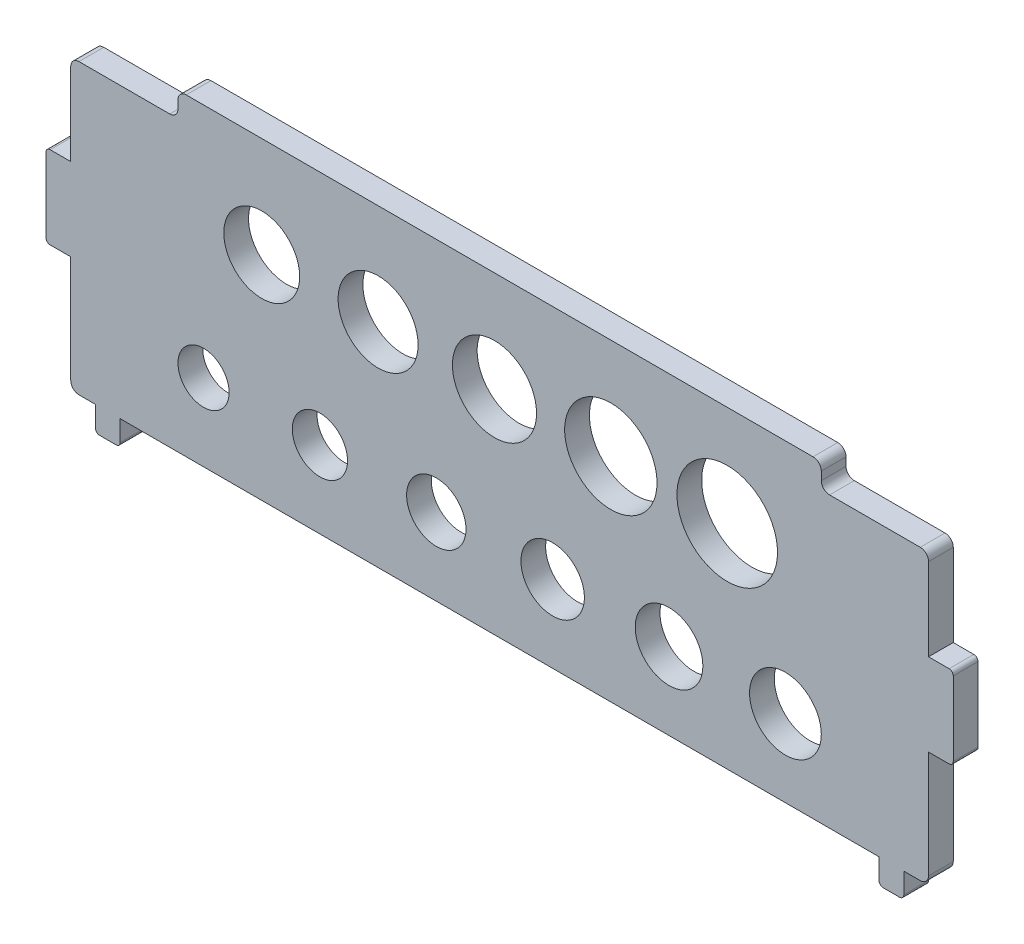
SolidWorks part; units mm, degrees
ref_plane "Спереди" through (0, 0, 0) normal (0, 0, 1) x (1, 0, 0)
ref_plane "Сверху" through (0, 0, 0) normal (0, 1, 0) x (1, 0, 0)
ref_plane "Справа" through (0, 0, 0) normal (1, 0, 0) x (0, 0, -1)
sketch "Эскиз1" plane through (0, 0, 0) normal (0, 0, 1) x (1, 0, 0)
  line L0 (0, 0) -> (0, 25.1439) construction
  line L1 (-52, 19) -> (52, 19)
  line L2 (-52, 19) -> (-52, -19)
  line L3 (-52, -19) -> (-49, -19)
  line L4 (52, 19) -> (52, -19)
  line L5 (-52, 19) -> (52, -19) construction
  line L6 (-52, -19) -> (52, 19) construction
  line L7 (52, 5) -> (55, 5)
  line L8 (52, 5) -> (52, -5)
  line L9 (52, -5) -> (55, -5)
  line L10 (55, 5) -> (55, -5)
  line L11 (52, 5) -> (55, -5) construction
  line L12 (52, -5) -> (55, 5) construction
  line L13 (-52, -5) -> (-55, 5) construction
  line L14 (-52, 5) -> (-55, -5) construction
  line L15 (-55, 5) -> (-55, -5)
  line L16 (-52, -5) -> (-55, -5)
  line L17 (-52, 5) -> (-52, -5)
  line L18 (-52, 5) -> (-55, 5)
  line L19 (-52, 16) -> (-39, 16)
  line L20 (-39, 16) -> (-39, 19)
  line L21 (39, 16) -> (39, 19)
  line L22 (52, 16) -> (39, 16)
  line L23 (27.595, 6.8) -> (27.595, -9.65) construction
  line L24 (27.595, 6.8) -> (13.485, 6.8) construction
  line L25 (13.485, 6.8) -> (-0.625, 6.8) construction
  line L26 (-0.625, 6.8) -> (-14.735, 6.8) construction
  line L27 (-14.735, 6.8) -> (-28.845, 6.8) construction
  line L28 (34.65, -9.65) -> (20.54, -9.65) construction
  line L29 (20.54, -9.65) -> (6.43, -9.65) construction
  line L30 (6.43, -9.65) -> (-7.68, -9.65) construction
  line L31 (-7.68, -9.65) -> (-21.79, -9.65) construction
  line L32 (-21.79, -9.65) -> (-35.9, -9.65) construction
  line L33 (0, -19) -> (46, -19)
  line L38 (49, -19) -> (52, -19)
  line L39 (-46, -19) -> (0, -19)
  line L40 (-49, -22) -> (-46, -19) construction
  line L42 (49, -19) -> (49, -22)
  line L43 (49, -22) -> (46, -22)
  line L44 (46, -19) -> (46, -22)
  line L45 (49, -19) -> (46, -22) construction
  line L46 (49, -22) -> (46, -19) construction
  line L47 (-49, -19) -> (-46, -22) construction
  line L48 (-46, -19) -> (-46, -22)
  line L49 (-49, -22) -> (-46, -22)
  line L50 (-49, -19) -> (-49, -22)
  circle A18 centre (27.595, 6.8) radius 6.1
  circle A19 centre (13.485, 6.8) radius 5.6
  circle A20 centre (-0.625, 6.8) radius 5.1
  circle A21 centre (-14.735, 6.8) radius 4.85
  circle A22 centre (-28.845, 6.8) radius 4.6
  circle A23 centre (34.65, -9.65) radius 4.35
  circle A24 centre (20.54, -9.65) radius 4.1
  circle A25 centre (6.43, -9.65) radius 3.85
  circle A26 centre (-7.68, -9.65) radius 3.6
  circle A27 centre (-21.79, -9.65) radius 3.35
  circle A28 centre (-35.9, -9.65) radius 3.1
  point P0 (0, 0)
  point P6 (53.5, 0)
  point P17 (-53.5, 0)
  point P29 (47.5, -20.5)
  point P61 (-47.5, -20.5)
  dimension "D5" = 13
  dimension "D7" = 11.2
  dimension "D6" = 12.2
  dimension "D8" = 10.2
  dimension "D11" = 9.7
  dimension "D15" = 9.2
  dimension "D16" = 8.7
  dimension "D17" = 8.2
  dimension "D18" = 7.7
  dimension "D19" = 7.2
  dimension "D20" = 6.7
  dimension "D21" = 6.2
  dimension "D9" = 13
  dimension "D10" = 5
  dimension "D14" = 6
  dimension "D1" = 3
  dimension "D2" = 10
  dimension "D3" = 38
  dimension "D4" = 110
  dimension "D12" = 13
  dimension "D13" = 3
  dimension "D22" = 3
  dimension "D24" = 3
  dimension "D25" = 3
extrude "Бобышка-Вытянуть1" add sketch "Эскиз1" along normal blind 3
fillet "Скругление1" radius 0.5 8 edges at (-55, 5, 1.5) (-55, -5, 1.5) (55, -5, 1.5) (55, 5, 1.5) (-46, -22, 1.5) (-49, -22, 1.5) (49, -22, 1.5) (46, -22, 1.5)
fillet "Скругление2" radius 1 8 edges at (-52, -19, 1.5) (-52, 16, 1.5) (-39, 16, 1.5) (-39, 19, 1.5) (39, 19, 1.5) (39, 16, 1.5) (52, 16, 1.5) (52, -19, 1.5)
equation "\"a\"= 0 , 2"
